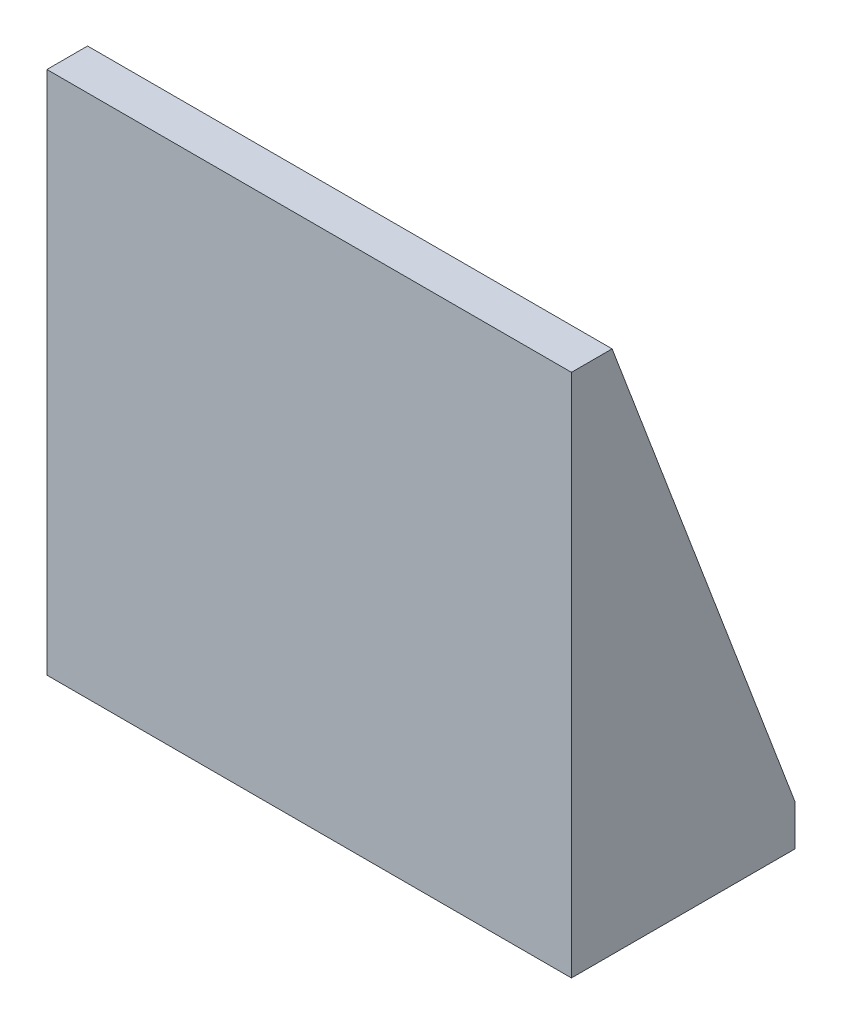
SolidWorks part; units mm, degrees
ref_plane "Front" through (0, 0, 0) normal (0, 0, 1) x (1, 0, 0)
ref_plane "Top" through (0, 0, 0) normal (0, 1, 0) x (1, 0, 0)
ref_plane "Right" through (0, 0, 0) normal (1, 0, 0) x (0, 0, -1)
sketch "Sketch1" plane through (0, 0, 0) normal (1, 0, 0) x (0, 0, -1)
  line L0 (0, 0) -> (55, 0)
  line L1 (0, 0) -> (0, 129)
  dimension "D1" = 129
  dimension "D2" = 55
extrude "Extrude-Thin1" add sketch "Sketch1" along normal mid plane 129 thin thin type one direction wall 10
sketch "Sketch2" plane through (64.5, 0, 0) normal (1, 0, 0) x (0, 0, -1)
  line L0 (10, 129) -> (55, 10)
  line L1 (55, 10) -> (10, 10) construction
  line L2 (55, 10) -> (10, 10)
  line L3 (10, 10) -> (10, 129) construction
  line L4 (10, 10) -> (10, 129)
extrude "Extrude1" add sketch "Sketch2" against normal blind 10
mirror "Mirror1" about plane through (0, 0, 0) normal (1, 0, 0) of "Extrude1"
